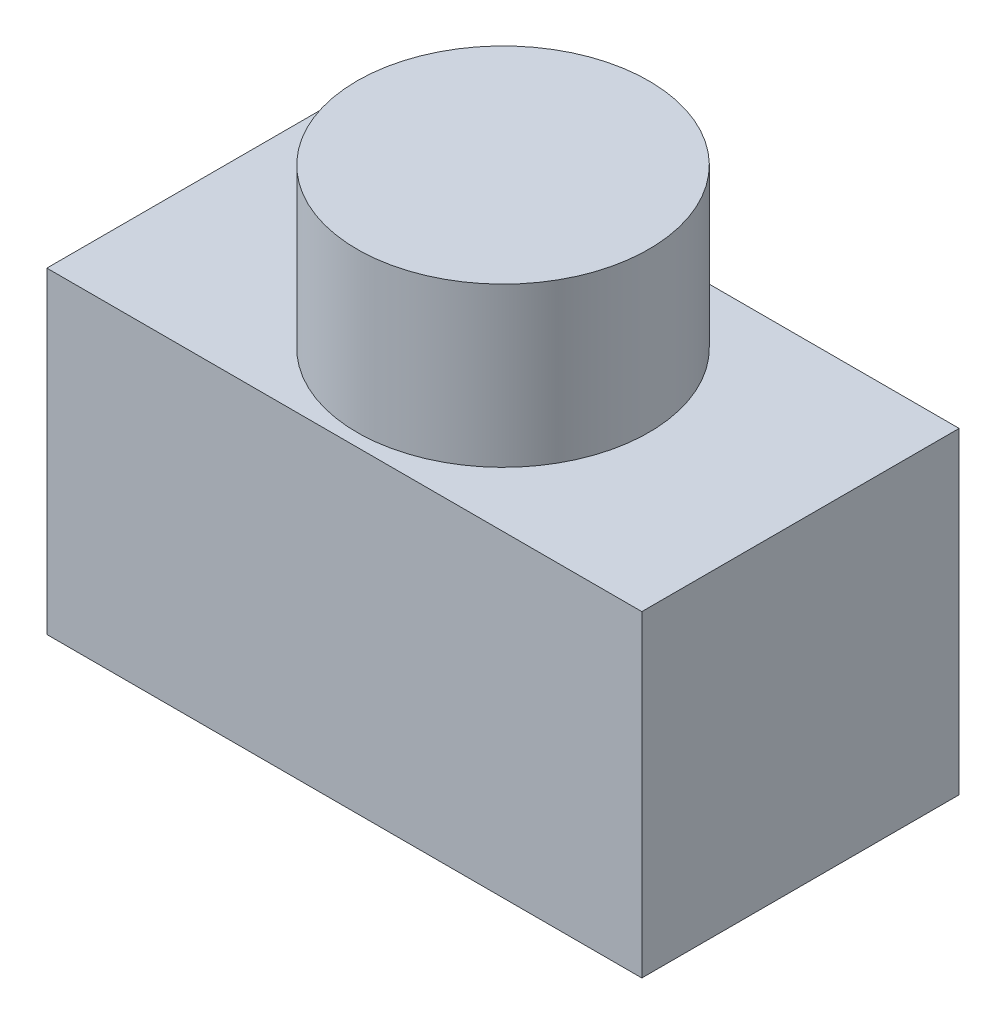
SolidWorks part; units mm, degrees
ref_plane "Ebene vorne" through (0, 0, 0) normal (0, 0, 1) x (1, 0, 0)
ref_plane "Ebene oben" through (0, 0, 0) normal (0, 1, 0) x (1, 0, 0)
ref_plane "Ebene rechts" through (0, 0, 0) normal (1, 0, 0) x (0, 0, -1)
sketch "Skizze1" plane through (0, 0, 0) normal (0, 0, 1) x (1, 0, 0)
  line L0 (-90.0474, 0) -> (53.2701, 0) construction
  line L1 (0, 45.9716) -> (0, -47.6777) construction
  line L3 (-37.5, 20) -> (37.5, 20)
  line L4 (-37.5, 20) -> (-37.5, -20)
  line L5 (-37.5, -20) -> (37.5, -20)
  line L6 (37.5, 20) -> (37.5, -20)
  line L7 (-37.5, 20) -> (37.5, -20) construction
  line L8 (-37.5, -20) -> (37.5, 20) construction
  point P5 (0, 0)
  dimension "D1" = 40
  dimension "D2" = 75
extrude "Aufsatz-Linear austragen1" add sketch "Skizze1" along normal blind 40
sketch "Skizze2" plane through (0, 0, 0) normal (0, 0, -1) x (-1, 0, 0)
  circle A0 centre (0, 0) radius 18.39
  dimension "D1" = 36.78
extrude "Aufsatz-Linear austragen2" add sketch "Skizze2" along normal blind 20 contours A0
move or copy body "Körper-Verschieben/Kopieren1" bodies to move or copy 102 copy no rotation origin (0, 0, 10) rotation axis (1, 0, 0) rotation angle 180
move or copy body "Körper-Verschieben/Kopieren2" bodies to move or copy 103 copy no rotation origin (0, 0, 10) rotation axis (1, 0, 0) rotation angle 90
move or copy body "Körper-Verschieben/Kopieren3" bodies to move or copy 104 copy no rotation origin (0, 0, 10) rotation axis (1, 0, 0) rotation angle 180
move or copy body "Körper-Verschieben/Kopieren4" bodies to move or copy 105 copy no translate (0, -10, 0)
move or copy body "Körper-Verschieben/Kopieren5" bodies to move or copy 106 copy no translate (0, 0, -10)
